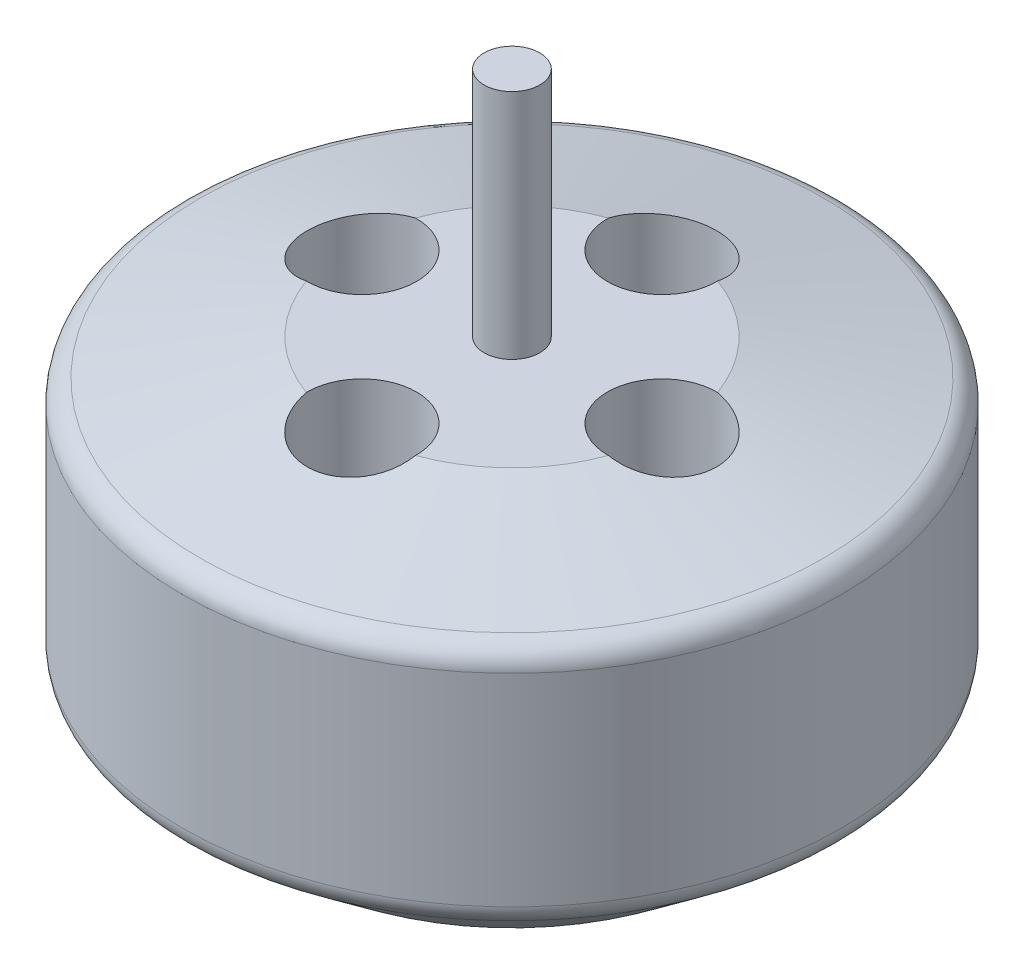
SolidWorks part; units mm, degrees
ref_plane "Front Plane" through (0, 0, 0) normal (0, 0, 1) x (1, 0, 0)
ref_plane "Top Plane" through (0, 0, 0) normal (0, 1, 0) x (1, 0, 0)
ref_plane "Right Plane" through (0, 0, 0) normal (1, 0, 0) x (0, 0, -1)
sketch "Sketch2" plane through (0, 0, 0) normal (0, 0, 1) x (1, 0, 0)
  line L0 (0, 9.2312) -> (0, -15.7688)
  line L1 (0, -15.7688) -> (10, -15.7688)
  line L2 (10, -15.7688) -> (14.2142, -12.4957)
  line L3 (14.2142, -12.4957) -> (14.2142, -2.4957)
  line L5 (1.2, -0.7688) -> (1.2, 9.2312)
  line L6 (1.2, 9.2312) -> (0, 9.2312)
  line L7 (1.2, -0.7688) -> (6.9234, -0.7688)
  line L8 (6.9234, -0.7688) -> (14.2142, -2.4957)
  dimension "D1" = 1.2
  dimension "D2" = 25
  dimension "D3" = 10
  dimension "D4" = 15
  dimension "D5" = 10
revolve "Revolve1" add sketch "Sketch2" angle 360 about L0
ref_plane "Plane1" through (0, 4.6156, 0) normal (0, 1, 0) x (1, 0, 0)
sketch "Sketch3" plane through (0, 4.6156, 0) normal (0, 1, 0) x (1, 0, 0)
  circle A0 centre (0, -6.4704) radius 2.3523
extrude "Cut-Extrude1" cut sketch "Sketch3" against normal blind 10
pattern_circular "CirPattern1" count 4 over 360 about axis through (0, 0, 0) along (0, 1, 0) of "Cut-Extrude1"
fillet "Fillet1" radius 1 2 edges at (-14.2142, -12.4957, 0) (-14.2142, -2.4957, 0)
